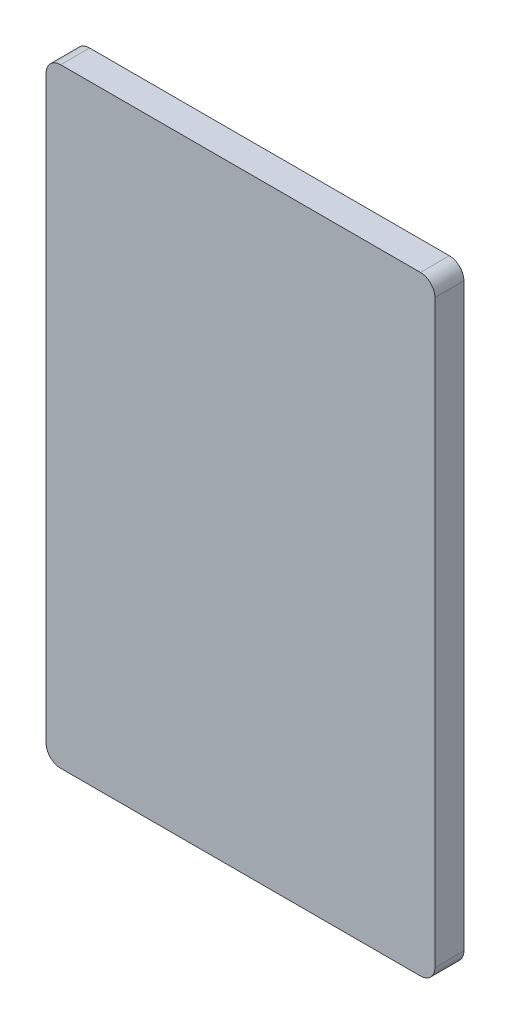
SolidWorks part; units mm, degrees
material "有机玻璃 (TM) GS 丙烯酸铸钣"
ref_plane "前视基准面" through (0, 0, 0) normal (0, 0, 1) x (1, 0, 0)
ref_plane "上视基准面" through (0, 0, 0) normal (0, 1, 0) x (1, 0, 0)
ref_plane "右视基准面" through (0, 0, 0) normal (1, 0, 0) x (0, 0, -1)
sketch "草图2" plane through (0, 0, 0) normal (0, 0, 1) x (1, 0, 0)
  line L5 (0, 0) -> (57.1502, 0) construction
  line L6 (0, 0) -> (0, 95.2498) construction
  line L7 (0, 95.2498) -> (57.1502, 95.2498) construction
  line L8 (57.1502, 0) -> (57.1502, 95.2498) construction
  line L9 (2.5, 0) -> (64.6586, 0)
  line L10 (0, 2.5) -> (0, 102.7498)
  line L11 (2.5, 105.2498) -> (64.6586, 105.2498)
  line L12 (67.1586, 2.5) -> (67.1586, 102.7498)
  arc A6 (0, 2.5) -> (2.5, 0) centre (2.5, 2.5) ccw
  arc A7 (64.6586, 0) -> (67.1586, 2.5) centre (64.6586, 2.5) ccw
  arc A8 (67.1586, 102.7498) -> (64.6586, 105.2498) centre (64.6586, 102.7498) ccw
  arc A9 (2.5, 105.2498) -> (0, 102.7498) centre (2.5, 102.7498) ccw
  dimension "D1" = 2.5
extrude "凸台-拉伸2" add sketch "草图2" along normal blind 5
